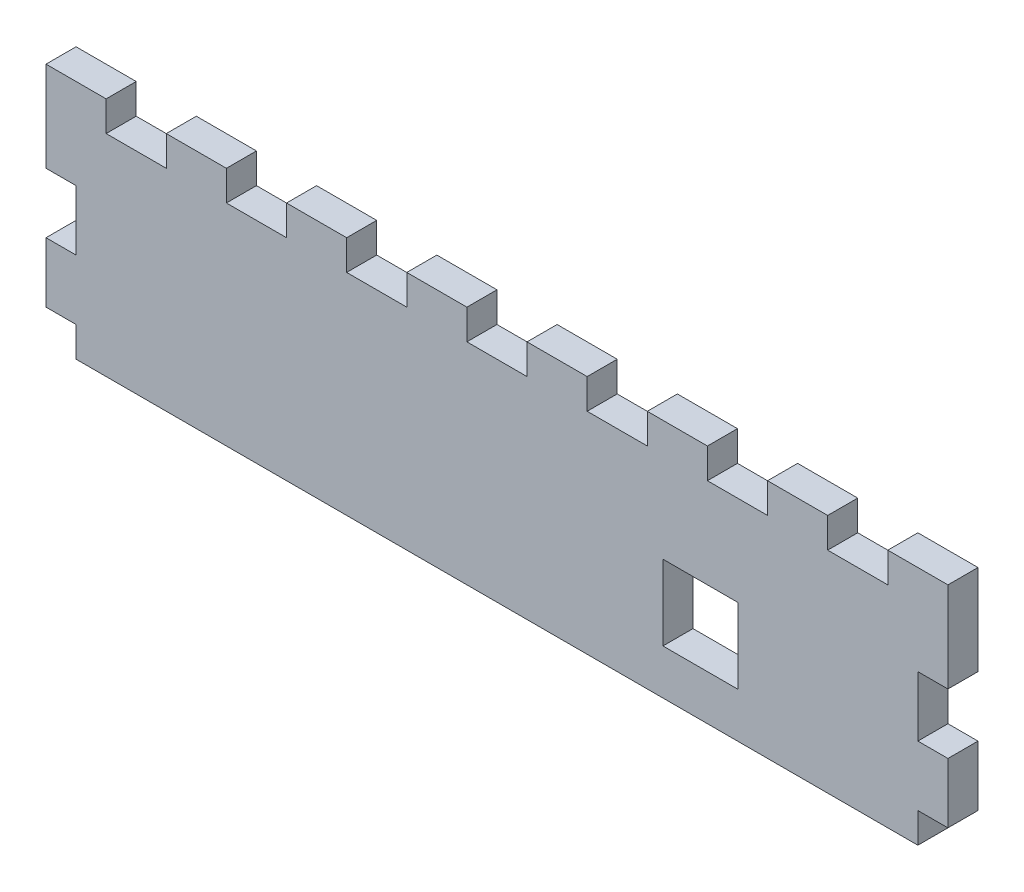
SolidWorks part; units mm, degrees
ref_plane "Front Plane" through (0, 0, 0) normal (0, 0, 1) x (1, 0, 0)
ref_plane "Top Plane" through (0, 0, 0) normal (0, 1, 0) x (1, 0, 0)
ref_plane "Right Plane" through (0, 0, 0) normal (1, 0, 0) x (0, 0, -1)
sketch "Sketch1" plane through (0, 0, 0) normal (0, 0, 1) x (1, 0, 0)
  line L1 (-95.25, -25.4) -> (95.25, -25.4)
  line L2 (-95.25, -25.4) -> (-95.25, 25.4)
  line L3 (-95.25, 25.4) -> (95.25, 25.4)
  line L4 (95.25, -25.4) -> (95.25, 25.4)
  line L5 (-95.25, -25.4) -> (95.25, 25.4) construction
  line L6 (-95.25, 25.4) -> (95.25, -25.4) construction
  point P0 (0, 0)
  dimension "D1" = 50.8
  dimension "D2" = 190.5
extrude "Boss-Extrude1" add sketch "Sketch1" along normal blind 6.35
sketch "Sketch2" plane through (0, 0, 6.35) normal (0, 0, 1) x (1, 0, 0)
  line L0 (-95.25, 25.4) -> (-95.25, -25.4) construction
  line L1 (-95.25, -6.35) -> (-88.9, -6.35)
  line L2 (-95.25, -6.35) -> (-95.25, 6.35)
  line L3 (-95.25, 6.35) -> (-88.9, 6.35)
  line L4 (-88.9, -6.35) -> (-88.9, 6.35)
  dimension "D1" = 6.35
  dimension "D2" = 12.7
  dimension "D3" = 19.05
extrude "Cut-Extrude1" cut sketch "Sketch2" against normal through all
sketch "Sketch3" plane through (0, 0, 6.35) normal (0, 0, 1) x (1, 0, 0)
  line L1 (-95.25, -25.4) -> (-88.9, -25.4)
  line L2 (-95.25, -25.4) -> (-95.25, -19.05)
  line L3 (-95.25, -19.05) -> (-88.9, -19.05)
  line L4 (-88.9, -25.4) -> (-88.9, -19.05)
  dimension "D1" = 6.35
  dimension "D2" = 6.35
extrude "Cut-Extrude2" cut sketch "Sketch3" against normal through all
mirror "Mirror1" about plane through (0, 0, 0) normal (1, 0, 0) of "Cut-Extrude2"
mirror "Mirror2" about plane through (0, 0, 0) normal (1, 0, 0) of "Cut-Extrude1"
sketch "Sketch4" plane through (0, 0, 6.35) normal (0, 0, 1) x (1, 0, 0)
  line L0 (95.25, 25.4) -> (-95.25, 25.4) construction
  line L1 (-82.55, 25.4) -> (-69.85, 25.4)
  line L2 (-82.55, 25.4) -> (-82.55, 19.05)
  line L3 (-82.55, 19.05) -> (-69.85, 19.05)
  line L4 (-69.85, 25.4) -> (-69.85, 19.05)
  dimension "D1" = 12.7
  dimension "D2" = 6.35
  dimension "D3" = 12.7
extrude "Cut-Extrude3" cut sketch "Sketch4" against normal through all
pattern_linear "LPattern1" count 7 spacing 25.4 along (1, 0, 0) of "Cut-Extrude3"
sketch "Sketch5" plane through (0, 0, 6.35) normal (0, 0, 1) x (1, 0, 0)
  line L1 (35.052, 0) -> (50.927, 0)
  line L2 (35.052, 0) -> (35.052, -15.875)
  line L3 (35.052, -15.875) -> (50.927, -15.875)
  line L4 (50.927, 0) -> (50.927, -15.875)
  dimension "D1" = 15.875
  dimension "D2" = 15.875
  dimension "D3" = 19.05
  dimension "D4" = 123.952
  dimension "D5" = 37.973
extrude "Cut-Extrude4" cut sketch "Sketch5" against normal through all
